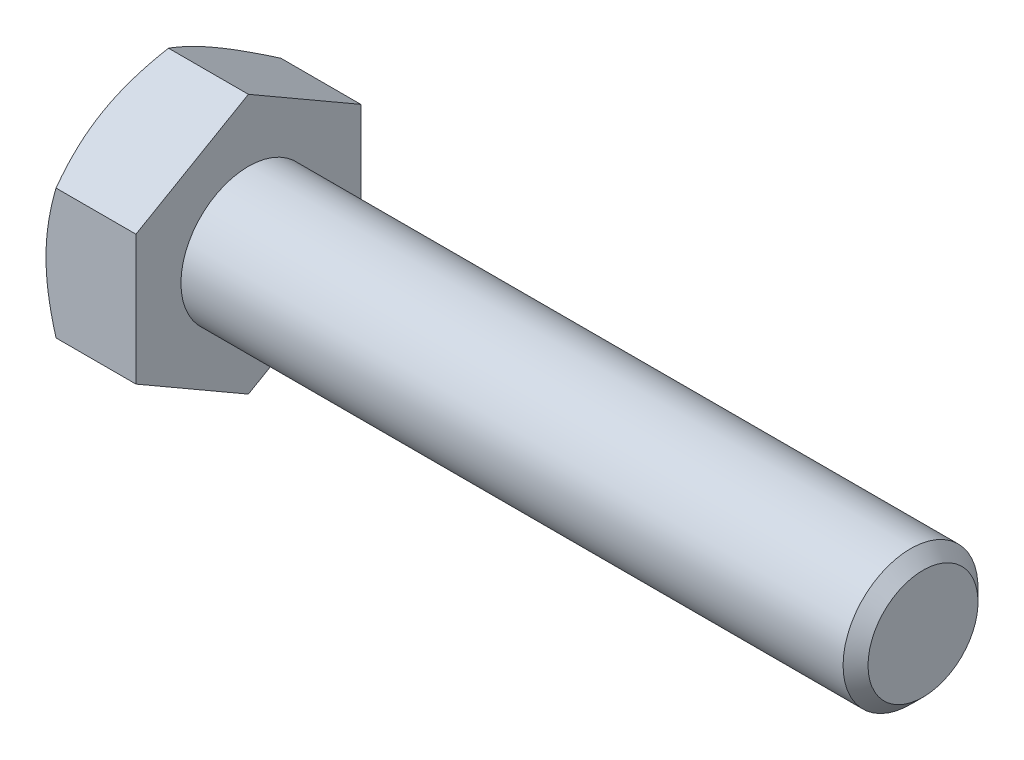
SolidWorks part; units mm, degrees
ref_plane "Plane1" through (0, 0, 0) normal (0, 0, 1) x (1, 0, 0)
ref_plane "Plane2" through (0, 0, 0) normal (0, 1, 0) x (1, 0, 0)
ref_plane "Plane3" through (0, 0, 0) normal (1, 0, 0) x (0, 0, -1)
sketch "Sketch1" plane through (0, 0, 0) normal (1, 0, 0) x (0, 0, -1)
  line L0 (5, 2.8868) -> (5, -2.8868)
  line L1 (-5, 2.8868) -> (-5, -2.8868)
  line L2 (5, -2.8868) -> (0, -5.7735)
  line L3 (0, -5.7735) -> (-5, -2.8868)
  line L4 (5, 2.8868) -> (0, 5.7735)
  line L5 (0, 5.7735) -> (-5, 2.8868)
  dimension "Width_flats" = 10
  dimension "D2" = 120
  dimension "D3" = 5
  dimension "D4" = 5
  dimension "D5" = 5
extrude "BaseHead" add sketch "Sketch1" along normal blind 4
sketch "BodySke" plane through (0, 0, 0) normal (0, 0, 1) x (1, 0, 0)
  line L1 (0, 0) -> (34, 0)
  line L2 (0, 0) -> (0, 3)
  line L4 (34, 0) -> (34, 2.4455)
  line L5 (4, 5.7735) -> (4, 2.8868) construction
  line L6 (34, 2.4455) -> (33.4455, 3)
  line L7 (0, 0) -> (110.49, 0) construction
  line L8 (34, -2.4455) -> (33.4455, -3) construction
  line L9 (0, 2.8868) -> (0, -2.8868) construction
  line L10 (5, 15.24) -> (5, -1.27) construction
  line L11 (4, 15.24) -> (4, -1.27) construction
  line L12 (4, 2.8868) -> (4, -2.8868) construction
  line L15 (0, 3) -> (33.4455, 3)
  dimension "Length" = 30
  dimension "Body_ch_ang" = 45
  dimension "Diameter" = 6
  dimension "Minor_dia" = 4.891
  dimension "Advance" = 1
  dimension "Thread_nom" = 30
revolve "BaseBody" add sketch "BodySke" angle 360 about L7
cosmetic thread "ThreadCosmetic" [suppressed] parameters "Thread_length"=29, "Thread_minor"=4.891
fillet "HeadFillet" [suppressed] radius 0.25
sketch "Sketch3" plane through (0, 0, 0) normal (0, 0, 1) x (1, 0, 0)
  line L0 (0, 5) -> (3.3333, 10.7735)
  line L1 (0, 5.7735) -> (0, 2.8868) construction
  line L2 (3.3333, 10.7735) -> (3.3333, 15.7735)
  line L3 (3.3333, 15.7735) -> (-10, 15.7735)
  line L4 (-10, 15.7735) -> (-10, 5)
  line L5 (-10, 5) -> (0, 5)
  line L6 (0, 0) -> (99.06, 0) construction
  line L7 (4, 5.7735) -> (0, 5.7735) construction
  dimension "D1" = 5
  dimension "D2" = 5
  dimension "D3" = 10
  dimension "D4" = 5
  dimension "Head_ch_ang" = 30
revolve "HeadChamfer" cut sketch "Sketch3" angle 360 about L6
sketch "ThdSchSke" [suppressed] plane through (0, 0, 0) normal (0, 0, 1) x (1, 0, 0)
  line L0 (56.5, -8.626) -> (55.5379, -10)
  line L1 (56.5, -8.626) -> (57.4621, -10)
  line L2 (57.4621, -10) -> (57.4621, -12.5)
  line L3 (-3.175, 0) -> (5.1513, 0) construction
  line L5 (57.4621, -12.5) -> (55.5379, -12.5)
  line L6 (55.5379, -12.5) -> (55.5379, -10)
  dimension "Thread_minor" = 4.891
  dimension "Diameter" = 6
  dimension "Start" = 5
  dimension "SideAngle" = 55
  dimension "VeeAngle" = 70
  dimension "Overcut" = 7.5
revolve "ThreadSchematic" [suppressed] cut sketch "ThdSchSke" angle 360 about L3
pattern_linear "ThdSchPat" [suppressed]
equation "\"D3@Sketch1\" = \"Width_flats@Sketch1\" / 2"
equation "\"D4@Sketch1\" = \"D3@Sketch1\""
equation "\"D5@Sketch1\" = \"D4@Sketch1\""
equation "\"Thread_minor@ThreadCosmetic\" = \"Minor_dia@BodySke\""
equation "\"D1@Sketch3\" = \"Width_flats@Sketch1\" / 2"
equation "\"Thread_length@ThreadCosmetic\" = ((sgn( (\"Length@BodySke\" - \"Advance@BodySke\" ) - \"Thread_nom@BodySke\" )-1)*( (\"Length@BodySke\" - \"Advance@BodySke\" ) - \"Thread_nom@BodySke\" ))/-2+ \"Thread_nom@BodySke\""
equation "\"Thread_minor@ThdSchSke\" = \"Minor_dia@BodySke\""
equation "\"Diameter@ThdSchSke\" = \"Diameter@BodySke\""
equation "\"Overcut@ThdSchSke\" = \"Diameter@BodySke\" * 1.25"
equation "\"Start@ThdSchSke\" = \"Head_ht@BaseHead\" + \"Length@BodySke\" - \"Thread_length@ThreadCosmetic\"  '---Non-countersunk---"
equation "\"Num_threads@ThdSchPat\" = int( \"Thread_length@ThreadCosmetic\" / \"Advance@BodySke\" + 0.999 )  + 1"
equation "\"Advance@ThdSchPat\" = \"Thread_length@ThreadCosmetic\" /  (\"Num_threads@ThdSchPat\" - 1) 'relax it"
equation "\"Num_threads@ThdSchPat\" = \"Num_threads@ThdSchPat\" - sgn( \"Num_threads@ThdSchPat\" - 1) '---chamfered tips only---"
